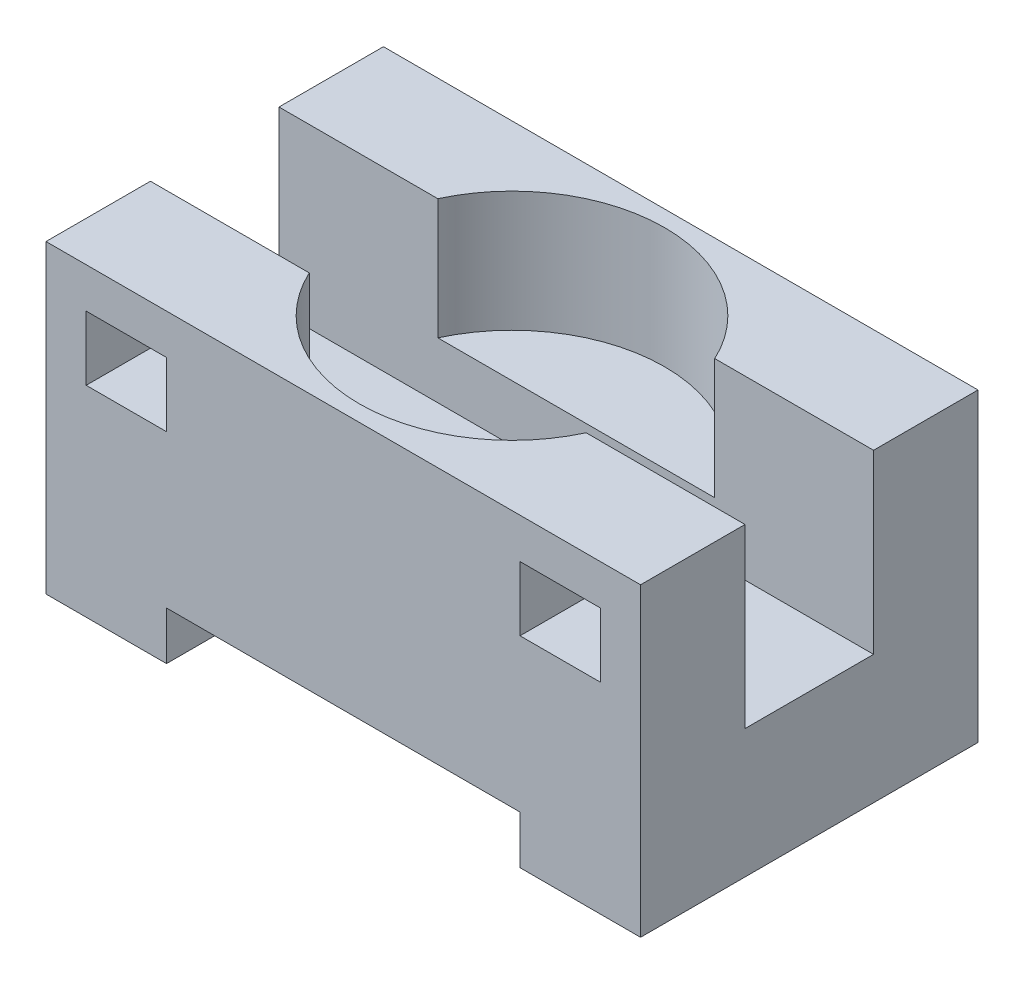
SolidWorks part; units mm, degrees
ref_plane "Front Plane" through (0, 0, 0) normal (0, 0, 1) x (1, 0, 0)
ref_plane "Top Plane" through (0, 0, 0) normal (0, 1, 0) x (1, 0, 0)
ref_plane "Right Plane" through (0, 0, 0) normal (1, 0, 0) x (0, 0, -1)
sketch "Sketch1" plane through (0, 0, 0) normal (0, 0, 1) x (1, 0, 0)
  line L1 (-37, 19) -> (37, 19)
  line L2 (-37, 19) -> (-37, -19)
  line L3 (-37, -19) -> (37, -19)
  line L4 (37, 19) -> (37, -19)
  line L5 (-37, 19) -> (37, -19) construction
  line L6 (-37, -19) -> (37, 19) construction
  point P0 (0, 0)
  dimension "D1" = 38
  dimension "D2" = 74
extrude "Boss-Extrude1" add sketch "Sketch1" along normal blind 42
sketch "Sketch2" plane through (0, 0, 0) normal (0, 0, -1) x (-1, 0, 0)
  line L0 (37, -19) -> (-37, -19) construction
  line L1 (-22, -19) -> (22, -19)
  line L2 (-22, -19) -> (-22, -13)
  line L3 (-22, -13) -> (22, -13)
  line L4 (22, -19) -> (22, -13)
  line L5 (-37, -19) -> (-37, 19) construction
  dimension "D1" = 6
  dimension "D2" = 44
  dimension "D3" = 15
extrude "Cut-Extrude1" cut sketch "Sketch2" against normal blind 42
sketch "Sketch3" plane through (37, 0, 0) normal (1, 0, 0) x (0, 0, -1)
  line L0 (-42, 19) -> (0, 19) construction
  line L1 (-29, 19) -> (-13, 19)
  line L2 (-29, 19) -> (-29, -3)
  line L3 (-29, -3) -> (-13, -3)
  line L4 (-13, 19) -> (-13, -3)
  line L5 (-42, -19) -> (-42, 19) construction
  dimension "D1" = 16
  dimension "D2" = 22
  dimension "D3" = 13
extrude "Cut-Extrude2" cut sketch "Sketch3" against normal blind 74
ref_plane "Plane1" through (0, 19, 0) normal (0, 1, 0) x (1, 0, 0)
sketch "Sketch4" plane through (0, 19, 0) normal (0, 1, 0) x (1, 0, 0)
  line L0 (-37, 0) -> (37, -42) construction
  circle A0 centre (0, -21) radius 19
  dimension "D1" = 38
extrude "Cut-Extrude3" cut sketch "Sketch4" against normal blind 15
sketch "Sketch5" plane through (0, 0, 42) normal (0, 0, 1) x (1, 0, 0)
  line L0 (0, 0) -> (0, 19) construction
  line L1 (37, 19) -> (-37, 19) construction
  line L2 (-37, 19) -> (-37, -19) construction
  line L3 (-32, 14) -> (-22, 14)
  line L4 (-32, 14) -> (-32, 6)
  line L5 (-32, 6) -> (-22, 6)
  line L6 (-22, 14) -> (-22, 6)
  line L7 (22, 14) -> (22, 6)
  line L8 (32, 14) -> (22, 14)
  line L9 (32, 14) -> (32, 6)
  line L10 (32, 6) -> (22, 6)
  dimension "D1" = 5
  dimension "D2" = 5
  dimension "D3" = 8
  dimension "D4" = 10
extrude "Cut-Extrude4" cut sketch "Sketch5" against normal blind 15
